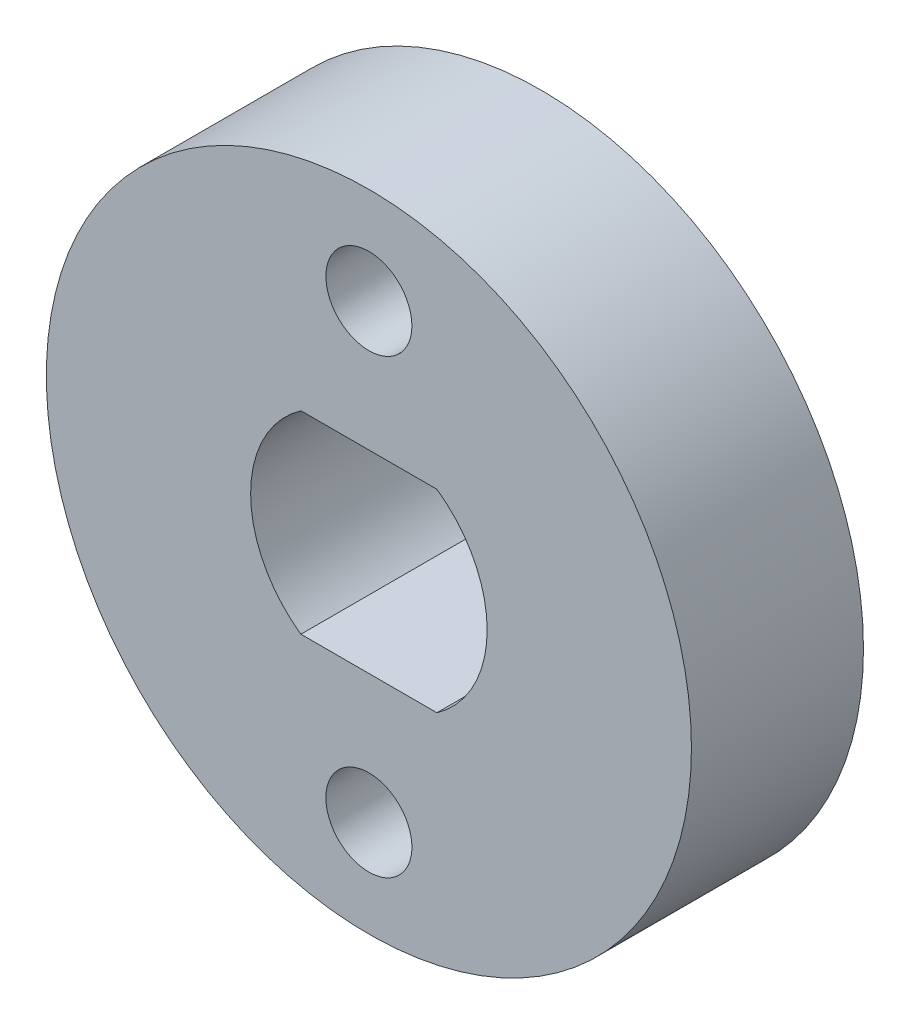
SolidWorks part; units mm, degrees
ref_plane "Спереди" through (0, 0, 0) normal (0, 0, 1) x (1, 0, 0)
ref_plane "Сверху" through (0, 0, 0) normal (0, 1, 0) x (1, 0, 0)
ref_plane "Справа" through (0, 0, 0) normal (1, 0, 0) x (0, 0, -1)
sketch "Эскиз1" plane through (0, 0, 0) normal (0, 0, 1) x (1, 0, 0)
  circle A0 centre (0, 0) radius 7.5
  dimension "D1" = 15
extrude "Бобышка-Вытянуть1" add sketch "Эскиз1" along normal blind 4 contours A0
sketch "Эскиз4" plane through (0, 0, 4) normal (0, 0, 1) x (1, 0, 0)
  line L0 (-1.5811, 2.25) -> (1.5811, 2.25)
  line L1 (-2.75, 0) -> (2.75, 0) construction
  line L2 (-1.5811, -2.25) -> (1.5811, -2.25)
  arc A0 (-1.5811, 2.25) -> (-1.5811, -2.25) centre (0, 0) ccw
  arc A1 (1.5811, -2.25) -> (1.5811, 2.25) centre (0, 0) ccw
  circle A2 centre (0, 5.25) radius 1
  circle A3 centre (0, -5.25) radius 1
  dimension "D1" = 5.5
  dimension "D3" = 2
  dimension "D4" = 10.5
  dimension "D2" = 4.5
extrude "Вырез-Вытянуть2" cut sketch "Эскиз4" against normal blind 4
